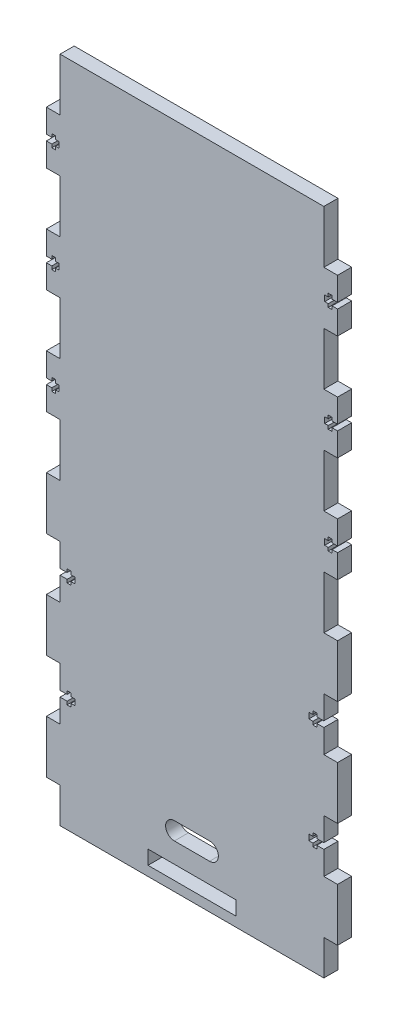
SolidWorks part; units mm, degrees
material "Acrylic (Medium-high impact)"
ref_plane "Front Plane" through (0, 0, 0) normal (0, 0, 1) x (1, 0, 0)
ref_plane "Top Plane" through (0, 0, 0) normal (0, 1, 0) x (1, 0, 0)
ref_plane "Right Plane" through (0, 0, 0) normal (1, 0, 0) x (0, 0, -1)
sketch "Sketch1" plane through (0, 0, 0) normal (0, 0, 1) x (1, 0, 0)
  line L1 (50, 13.5) -> (100, 13.5)
  line L2 (0, 0) -> (0, 380)
  line L3 (0, 380) -> (150, 380)
  line L4 (150, 0) -> (150, 380)
  line L5 (50, 13.5) -> (50, 5.5)
  line L6 (50, 5.5) -> (100, 5.5)
  line L7 (75, 0) -> (150, 0)
  line L8 (75, 0) -> (0, 0)
  line L9 (100, 13.5) -> (100, 5.5)
  dimension "D1" = 150
  dimension "D2" = 380
extrude "Boss-Extrude1" add sketch "Sketch1" along normal blind 8
sketch "Sketch2" plane through (0, 0, 8) normal (0, 0, 1) x (1, 0, 0)
  line L0 (150, 0) -> (150, 380) construction
  line L1 (150, 350) -> (157.8, 350)
  line L2 (150, 350) -> (150, 320)
  line L3 (150, 320) -> (157.8, 320)
  line L4 (157.8, 350) -> (157.8, 320)
  line L5 (150, 380) -> (0, 380) construction
  line L6 (0, 50) -> (-7.8, 50)
  line L7 (0, 50) -> (0, 20)
  line L8 (-7.8, 50) -> (-7.8, 20)
  line L9 (0, 20) -> (-7.8, 20)
  line L10 (0, 110) -> (-7.8, 110)
  line L11 (0, 110) -> (0, 80)
  line L12 (-7.8, 110) -> (-7.8, 80)
  line L13 (0, 80) -> (-7.8, 80)
  line L14 (0, 170) -> (-7.8, 170)
  line L15 (0, 170) -> (0, 140)
  line L16 (-7.8, 170) -> (-7.8, 140)
  line L17 (0, 140) -> (-7.8, 140)
  line L18 (0, 230) -> (-7.8, 230)
  line L19 (0, 230) -> (0, 200)
  line L20 (-7.8, 230) -> (-7.8, 200)
  line L21 (0, 200) -> (-7.8, 200)
  line L22 (75, 380) -> (75, 0) construction
  line L23 (0, 0) -> (150, 0) construction
  line L24 (0, 290) -> (-7.8, 290)
  line L25 (0, 290) -> (0, 260)
  line L26 (-7.8, 290) -> (-7.8, 260)
  line L27 (0, 260) -> (-7.8, 260)
  line L28 (-7.8, 350) -> (-7.8, 320)
  line L29 (0, 320) -> (-7.8, 320)
  line L30 (0, 350) -> (0, 320)
  line L31 (0, 350) -> (-7.8, 350)
  line L44 (150, 260) -> (157.8, 260)
  line L45 (157.8, 290) -> (157.8, 260)
  line L46 (150, 290) -> (150, 260)
  line L47 (150, 290) -> (157.8, 290)
  line L48 (150, 200) -> (157.8, 200)
  line L49 (157.8, 230) -> (157.8, 200)
  line L50 (150, 230) -> (150, 200)
  line L51 (150, 230) -> (157.8, 230)
  line L52 (150, 140) -> (157.8, 140)
  line L53 (157.8, 170) -> (157.8, 140)
  line L54 (150, 170) -> (150, 140)
  line L55 (150, 170) -> (157.8, 170)
  line L56 (150, 80) -> (157.8, 80)
  line L57 (157.8, 110) -> (157.8, 80)
  line L58 (150, 110) -> (150, 80)
  line L59 (150, 110) -> (157.8, 110)
  line L60 (150, 20) -> (157.8, 20)
  line L61 (157.8, 50) -> (157.8, 20)
  line L62 (150, 50) -> (150, 20)
  line L63 (150, 50) -> (157.8, 50)
  dimension "D1" = 30
  dimension "D2" = 7.8
  dimension "D3" = 30
  dimension "D4" = 6
extrude "Boss-Extrude2" add sketch "Sketch2" against normal blind 8
sketch "Sketch3" plane through (0, 0, 8) normal (0, 0, 1) x (1, 0, 0)
  line L0 (65, 30) -> (85, 30) construction
  line L1 (65, 35) -> (85, 35)
  line L2 (65, 25) -> (85, 25)
  line L3 (75, 380) -> (75, 0) construction
  line L4 (150, 380) -> (0, 380) construction
  line L5 (0, 0) -> (150, 0) construction
  line L6 (-7.8, 335) -> (157.8, 335) construction
  line L7 (150, 123.35) -> (150, 126.65)
  line L8 (157.8, 320) -> (157.8, 350) construction
  line L9 (157.8, 333.35) -> (157.8, 336.65)
  line L10 (157.8, 336.65) -> (154.7, 336.65)
  line L11 (154.7, 336.65) -> (154.7, 338.5)
  line L12 (154.7, 338.5) -> (152.5, 338.5)
  line L13 (152.5, 338.5) -> (152.5, 336.65)
  line L14 (152.5, 336.65) -> (150.5, 336.65)
  line L15 (150.5, 336.65) -> (150.5, 333.35)
  line L16 (152.5, 333.35) -> (150.5, 333.35)
  line L17 (152.5, 331.5) -> (152.5, 333.35)
  line L18 (154.7, 331.5) -> (152.5, 331.5)
  line L19 (154.7, 333.35) -> (154.7, 331.5)
  line L20 (157.8, 333.35) -> (154.7, 333.35)
  line L21 (150, 126.65) -> (146, 126.65)
  line L22 (150, 65) -> (0, 65) construction
  line L23 (150, 50) -> (150, 80) construction
  line L24 (0, 80) -> (0, 50) construction
  line L25 (146, 126.65) -> (146, 128.5)
  line L26 (146, 128.5) -> (143.8, 128.5)
  line L27 (143.8, 128.5) -> (143.8, 126.65)
  line L28 (143.8, 126.65) -> (141.5, 126.65)
  line L29 (141.5, 126.65) -> (141.5, 123.35)
  line L30 (143.8, 123.35) -> (141.5, 123.35)
  line L31 (143.8, 121.5) -> (143.8, 123.35)
  line L32 (146, 121.5) -> (143.8, 121.5)
  line L33 (146, 123.35) -> (146, 121.5)
  line L34 (150, 123.35) -> (146, 123.35)
  line L35 (0, 63.35) -> (4, 63.35)
  line L36 (4, 63.35) -> (4, 61.5)
  line L37 (4, 61.5) -> (6.2, 61.5)
  line L38 (6.2, 61.5) -> (6.2, 63.35)
  line L39 (6.2, 63.35) -> (8.5, 63.35)
  line L40 (8.5, 66.65) -> (8.5, 63.35)
  line L41 (6.2, 66.65) -> (8.5, 66.65)
  line L42 (6.2, 68.5) -> (6.2, 66.65)
  line L43 (4, 68.5) -> (6.2, 68.5)
  line L44 (4, 66.65) -> (4, 68.5)
  line L45 (0, 66.65) -> (4, 66.65)
  line L46 (0, 63.35) -> (0, 66.65)
  line L47 (0, 123.35) -> (4, 123.35)
  line L48 (4, 123.35) -> (4, 121.5)
  line L49 (4, 121.5) -> (6.2, 121.5)
  line L50 (6.2, 121.5) -> (6.2, 123.35)
  line L51 (6.2, 123.35) -> (8.5, 123.35)
  line L52 (8.5, 126.65) -> (8.5, 123.35)
  line L53 (6.2, 126.65) -> (8.5, 126.65)
  line L54 (6.2, 128.5) -> (6.2, 126.65)
  line L55 (4, 128.5) -> (6.2, 128.5)
  line L56 (4, 126.65) -> (4, 128.5)
  line L57 (0, 126.65) -> (4, 126.65)
  line L58 (0, 123.35) -> (0, 126.65)
  line L69 (-7.8, 333.35) -> (-4.7, 333.35)
  line L70 (-4.7, 333.35) -> (-4.7, 331.5)
  line L71 (-4.7, 331.5) -> (-2.5, 331.5)
  line L72 (-2.5, 331.5) -> (-2.5, 333.35)
  line L73 (-2.5, 333.35) -> (-0.5, 333.35)
  line L74 (-0.5, 336.65) -> (-0.5, 333.35)
  line L75 (-2.5, 336.65) -> (-0.5, 336.65)
  line L76 (-2.5, 338.5) -> (-2.5, 336.65)
  line L77 (-4.7, 338.5) -> (-2.5, 338.5)
  line L78 (-4.7, 336.65) -> (-4.7, 338.5)
  line L79 (-7.8, 336.65) -> (-4.7, 336.65)
  line L80 (-7.8, 333.35) -> (-7.8, 336.65)
  line L84 (150, 63.35) -> (150, 66.65)
  line L85 (150, 66.65) -> (146, 66.65)
  line L86 (146, 66.65) -> (146, 68.5)
  line L87 (146, 68.5) -> (143.8, 68.5)
  line L88 (143.8, 68.5) -> (143.8, 66.65)
  line L89 (143.8, 66.65) -> (141.5, 66.65)
  line L90 (141.5, 66.65) -> (141.5, 63.35)
  line L91 (143.8, 63.35) -> (141.5, 63.35)
  line L92 (143.8, 61.5) -> (143.8, 63.35)
  line L93 (146, 61.5) -> (143.8, 61.5)
  line L94 (146, 63.35) -> (146, 61.5)
  line L95 (150, 63.35) -> (146, 63.35)
  line L134 (157.8, 273.35) -> (157.8, 276.65)
  line L135 (157.8, 276.65) -> (154.7, 276.65)
  line L136 (154.7, 276.65) -> (154.7, 278.5)
  line L137 (154.7, 278.5) -> (152.5, 278.5)
  line L138 (152.5, 278.5) -> (152.5, 276.65)
  line L139 (152.5, 276.65) -> (150.5, 276.65)
  line L140 (150.5, 276.65) -> (150.5, 273.35)
  line L141 (152.5, 273.35) -> (150.5, 273.35)
  line L142 (152.5, 271.5) -> (152.5, 273.35)
  line L143 (154.7, 271.5) -> (152.5, 271.5)
  line L144 (154.7, 273.35) -> (154.7, 271.5)
  line L145 (157.8, 273.35) -> (154.7, 273.35)
  line L146 (-7.8, 273.35) -> (-4.7, 273.35)
  line L147 (-4.7, 273.35) -> (-4.7, 271.5)
  line L148 (-4.7, 271.5) -> (-2.5, 271.5)
  line L149 (-2.5, 271.5) -> (-2.5, 273.35)
  line L150 (-2.5, 273.35) -> (-0.5, 273.35)
  line L151 (-0.5, 276.65) -> (-0.5, 273.35)
  line L152 (-2.5, 276.65) -> (-0.5, 276.65)
  line L153 (-2.5, 278.5) -> (-2.5, 276.65)
  line L154 (-4.7, 278.5) -> (-2.5, 278.5)
  line L155 (-4.7, 276.65) -> (-4.7, 278.5)
  line L156 (-7.8, 276.65) -> (-4.7, 276.65)
  line L157 (-7.8, 273.35) -> (-7.8, 276.65)
  line L158 (-7.8, 275) -> (157.8, 275) construction
  line L159 (157.8, 213.35) -> (157.8, 216.65)
  line L160 (157.8, 216.65) -> (154.7, 216.65)
  line L161 (154.7, 216.65) -> (154.7, 218.5)
  line L162 (154.7, 218.5) -> (152.5, 218.5)
  line L163 (152.5, 218.5) -> (152.5, 216.65)
  line L164 (152.5, 216.65) -> (150.5, 216.65)
  line L165 (150.5, 216.65) -> (150.5, 213.35)
  line L166 (152.5, 213.35) -> (150.5, 213.35)
  line L167 (152.5, 211.5) -> (152.5, 213.35)
  line L168 (154.7, 211.5) -> (152.5, 211.5)
  line L169 (154.7, 213.35) -> (154.7, 211.5)
  line L170 (157.8, 213.35) -> (154.7, 213.35)
  line L171 (-7.8, 213.35) -> (-4.7, 213.35)
  line L172 (-4.7, 213.35) -> (-4.7, 211.5)
  line L173 (-4.7, 211.5) -> (-2.5, 211.5)
  line L174 (-2.5, 211.5) -> (-2.5, 213.35)
  line L175 (-2.5, 213.35) -> (-0.5, 213.35)
  line L176 (-0.5, 216.65) -> (-0.5, 213.35)
  line L177 (-2.5, 216.65) -> (-0.5, 216.65)
  line L178 (-2.5, 218.5) -> (-2.5, 216.65)
  line L179 (-4.7, 218.5) -> (-2.5, 218.5)
  line L180 (-4.7, 216.65) -> (-4.7, 218.5)
  line L181 (-7.8, 216.65) -> (-4.7, 216.65)
  line L182 (-7.8, 213.35) -> (-7.8, 216.65)
  line L183 (-7.8, 215) -> (157.8, 215) construction
  arc A0 (65, 35) -> (65, 25) centre (65, 30) ccw
  arc A1 (85, 25) -> (85, 35) centre (85, 30) ccw
  point P2 (75, 30)
  point P27 (150.5, 335)
  point P47 (141.5, 125)
  point P75 (8.5, 65)
  point P76 (8.5, 125)
  point P97 (-0.5, 335)
  point P112 (141.5, 65)
  point P171 (150.5, 275)
  point P188 (-0.5, 275)
  point P199 (150.5, 215)
  point P216 (-0.5, 215)
  dimension "D2" = 5
  dimension "D1" = 20
  dimension "D3" = 25
  dimension "D4" = 3.3
  dimension "D5" = 7
  dimension "D6" = 2.2
  dimension "D7" = 2
  dimension "D8" = 4
  dimension "D9" = 2.2
  dimension "D10" = 2.3
  dimension "D11" = 3.3
  dimension "D12" = 7
  dimension "D14" = 0.5
  dimension "D13" = 3
extrude "Cut-Extrude1" cut sketch "Sketch3" against normal through all
